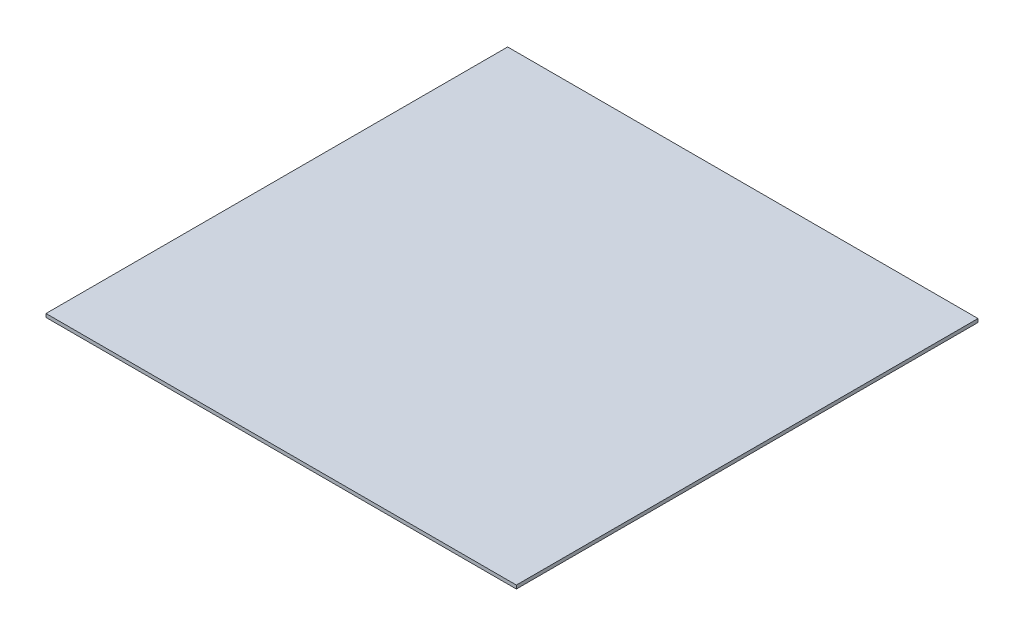
SolidWorks part; units mm, degrees
ref_plane "Front Plane" through (0, 0, 0) normal (0, 0, 1) x (1, 0, 0)
ref_plane "Top Plane" through (0, 0, 0) normal (0, 1, 0) x (1, 0, 0)
ref_plane "Right Plane" through (0, 0, 0) normal (1, 0, 0) x (0, 0, -1)
sketch "Sketch1" plane through (0, 0, 0) normal (0, 1, 0) x (1, 0, 0)
  line L1 (0, 0) -> (685.8, 0)
  line L2 (0, 0) -> (0, -673.1)
  line L3 (0, -673.1) -> (685.8, -673.1)
  line L4 (685.8, 0) -> (685.8, -673.1)
extrude "Boss-Extrude1" add sketch "Sketch1" along normal blind 5.08
